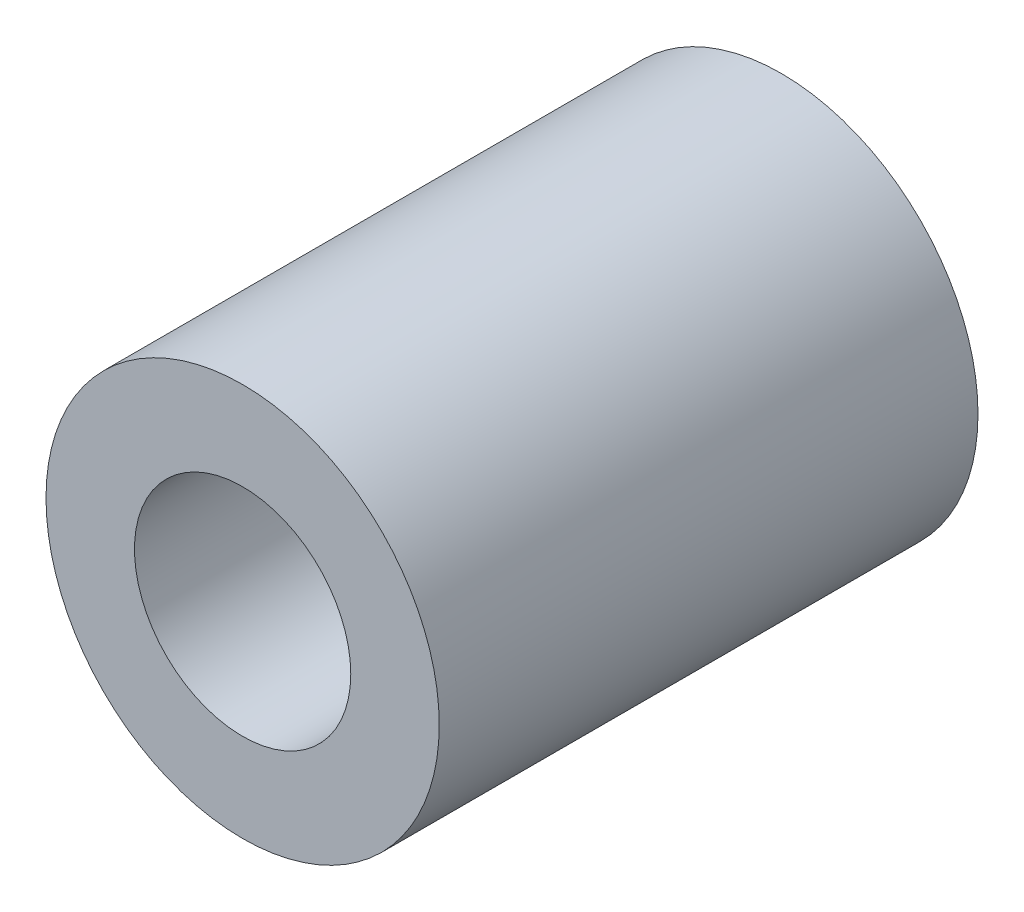
SolidWorks part; units mm, degrees
ref_plane "正面" through (0, 0, 0) normal (0, 0, 1) x (1, 0, 0)
ref_plane "平面" through (0, 0, 0) normal (0, 1, 0) x (1, 0, 0)
ref_plane "右側面" through (0, 0, 0) normal (1, 0, 0) x (0, 0, -1)
sketch "ｽｹｯﾁ1" plane through (0, 0, 0) normal (0, 0, 1) x (1, 0, 0)
  circle A0 centre (0, 0) radius 2.75
  circle A1 centre (0, 0) radius 5
  dimension "D1" = 5.5
  dimension "D2" = 10
extrude "ﾎﾞｽ - 押し出し1" add sketch "ｽｹｯﾁ1" along normal blind 13.7
